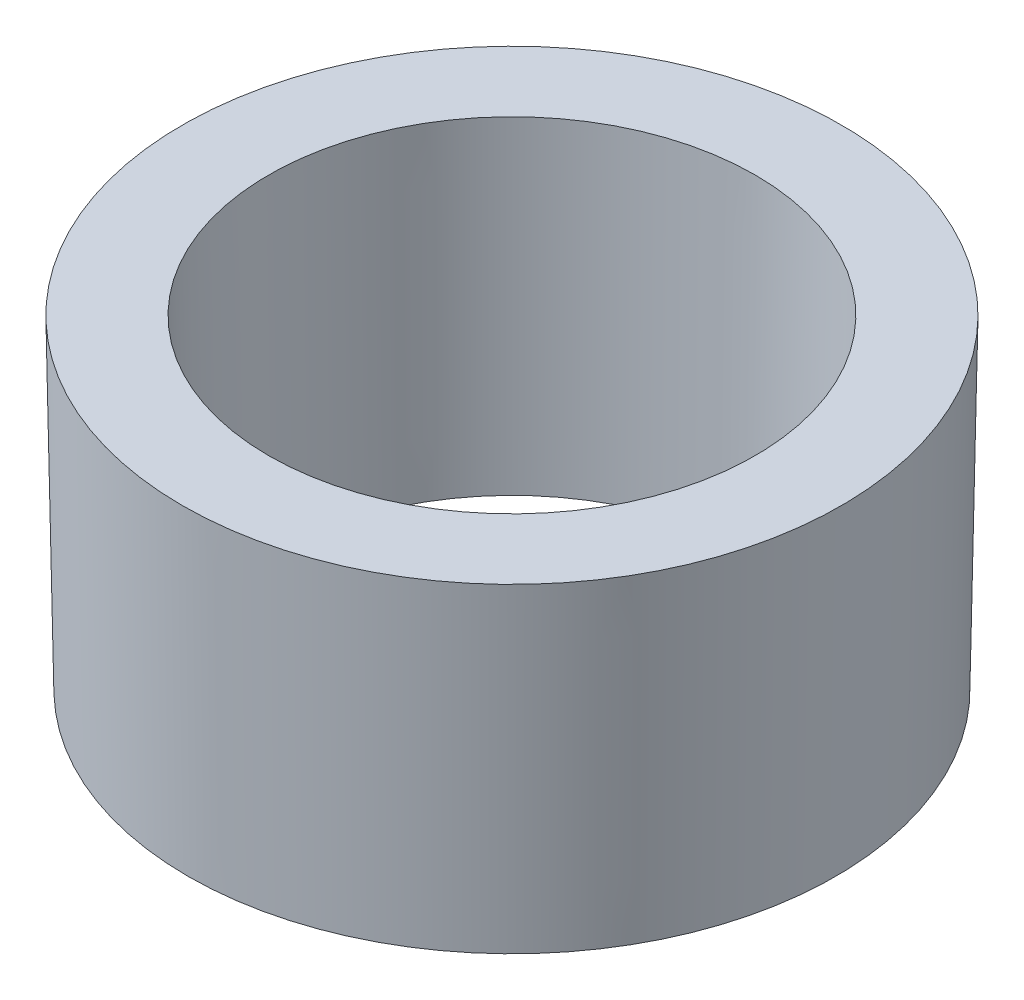
SolidWorks part; units mm, degrees
ref_plane "Front Plane" through (0, 0, 0) normal (0, 0, 1) x (1, 0, 0)
ref_plane "Top Plane" through (0, 0, 0) normal (0, 1, 0) x (1, 0, 0)
ref_plane "Right Plane" through (0, 0, 0) normal (1, 0, 0) x (0, 0, -1)
sketch "Sketch1" plane through (0, 0, 0) normal (0, 1, 0) x (1, 0, 0)
  circle A0 centre (0, 0) radius 15
  dimension "D1" = 30
extrude "Boss-Extrude1" add sketch "Sketch1" along normal blind 15 draft 1 draft outward yes
sketch "Sketch2" plane through (0, 0, 0) normal (0, -1, 0) x (1, 0, 0)
  circle A0 centre (0, 0) radius 11
  dimension "D1" = 22
extrude "Cut-Extrude1" cut sketch "Sketch2" against normal up to next (15 mm away) draft 1 draft outward yes
